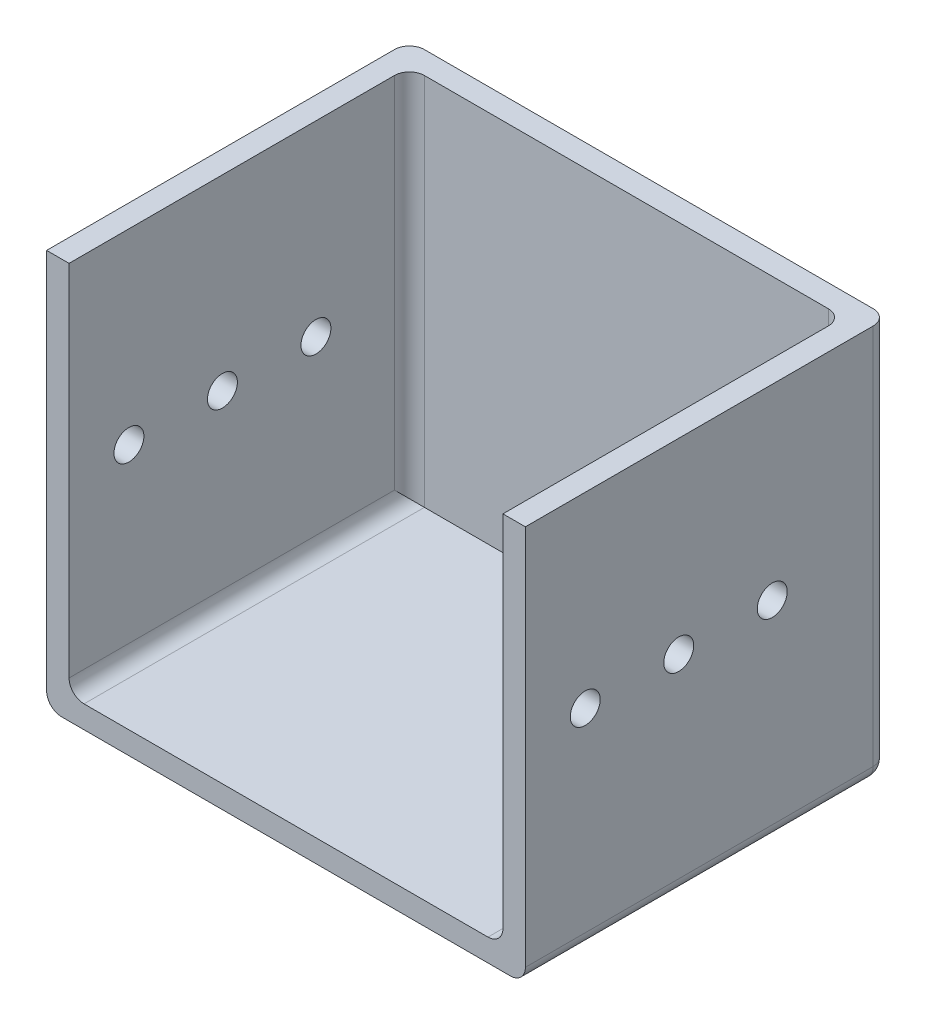
SolidWorks part; units mm, degrees
material "ABS"
ref_plane "Спереди" through (0, 0, 0) normal (0, 0, 1) x (1, 0, 0)
ref_plane "Сверху" through (0, 0, 0) normal (0, 1, 0) x (1, 0, 0)
ref_plane "Справа" through (0, 0, 0) normal (1, 0, 0) x (0, 0, -1)
other "Configuration Table"
sketch "Эскиз1" plane through (0, 0, 0) normal (0, 1, 0) x (1, 0, 0)
  line L1 (32, -24.25) -> (-32, -24.25)
  line L2 (32, -24.25) -> (32, 24.25)
  line L3 (32, 24.25) -> (-32, 24.25)
  line L4 (-32, -24.25) -> (-32, 24.25)
  line L5 (32, -24.25) -> (-32, 24.25) construction
  line L6 (32, 24.25) -> (-32, -24.25) construction
  point P0 (0, 0)
  dimension "D1" = 64
  dimension "D2" = 48.5
extrude "Бобышка-Вытянуть1" add sketch "Эскиз1" along normal blind 3
sketch "Эскиз2" plane through (0, 3, 0) normal (0, 1, 0) x (1, 0, 0)
  line L0 (-32, -24.25) -> (-32, 24.25)
  line L1 (-32, 24.25) -> (32, 24.25)
  line L2 (32, 24.25) -> (32, -24.25)
  line L3 (32, -24.25) -> (29, -24.25)
  line L4 (-32, -24.25) -> (32, -24.25) construction
  line L5 (-32, -24.25) -> (-29, -24.25)
  line L6 (-29, -24.25) -> (-29, 21.25)
  line L7 (-29, 21.25) -> (29, 21.25)
  line L8 (29, 21.25) -> (29, -24.25)
  dimension "D1" = 48.5
  dimension "D2" = 64
  dimension "D3" = 3
  dimension "D4" = 45.5
  dimension "D5" = 58
extrude "Бобышка-Вытянуть2" add sketch "Эскиз2" along normal blind 50
fillet "Скругление2" radius 2 1 edges at (0, 0, -24.25)
sketch "Эскиз3" plane through (32, 0, 0) normal (1, 0, 0) x (0, 0, -1)
  line L2 (-24.25, 0) -> (22.25, 0) construction
  line L3 (24.25, 53) -> (24.25, 2) construction
  circle A0 centre (8.75, 28) radius 2
  circle A1 centre (-3.75, 28) radius 2
  circle A2 centre (-16.25, 28) radius 2
  dimension "D1" = 4
  dimension "D2" = 28
  dimension "D3" = 15.5
  dimension "D4" = 3
extrude "Вырез-Вытянуть1" cut sketch "Эскиз3" against normal through all
fillet "Скругление3" radius 2 10 edges at (-32, 0, 1) (-32, 0.5858, -23.6642) (32, 0, 1) (32, 0.5858, -23.6642) (-29, 3, 1.5) (29, 3, 1.5) (-29, 28, -21.25) (29, 28, -21.25) (-32, 27.5, -24.25) (32, 27.5, -24.25)
